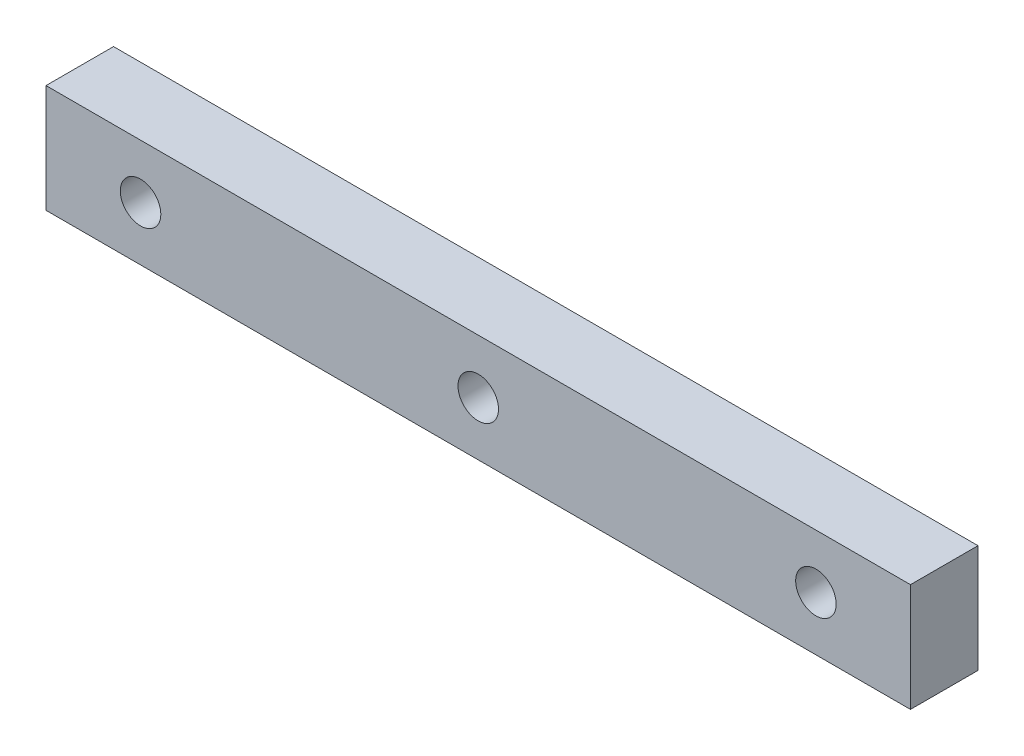
SolidWorks part; units mm, degrees
ref_plane "Front Plane" through (0, 0, 0) normal (0, 0, 1) x (1, 0, 0)
ref_plane "Top Plane" through (0, 0, 0) normal (0, 1, 0) x (1, 0, 0)
ref_plane "Right Plane" through (0, 0, 0) normal (1, 0, 0) x (0, 0, -1)
sketch "Sketch1" plane through (0, 0, 0) normal (0, 0, 1) x (1, 0, 0)
  line L1 (-32, 4) -> (32, 4)
  line L2 (-32, 4) -> (-32, -4)
  line L3 (-32, -4) -> (32, -4)
  line L4 (32, 4) -> (32, -4)
  dimension "D1" = 64
  dimension "D2" = 8
  dimension "D3" = 4
  dimension "D4" = 32
extrude "Boss-Extrude1" add sketch "Sketch1" along normal blind 5
sketch "Sketch2" plane through (0, 0, 0) normal (0, 0, -1) x (-1, 0, 0)
  circle A0 centre (-25, 0) radius 1.5
  circle A1 centre (0, 0) radius 1.5
  circle A2 centre (25, 0) radius 1.5
  dimension "D1" = 3
  dimension "D2" = 3
  dimension "D3" = 3
  dimension "D4" = 25
  dimension "D5" = 25
extrude "Cut-Extrude1" cut sketch "Sketch2" against normal blind 10
